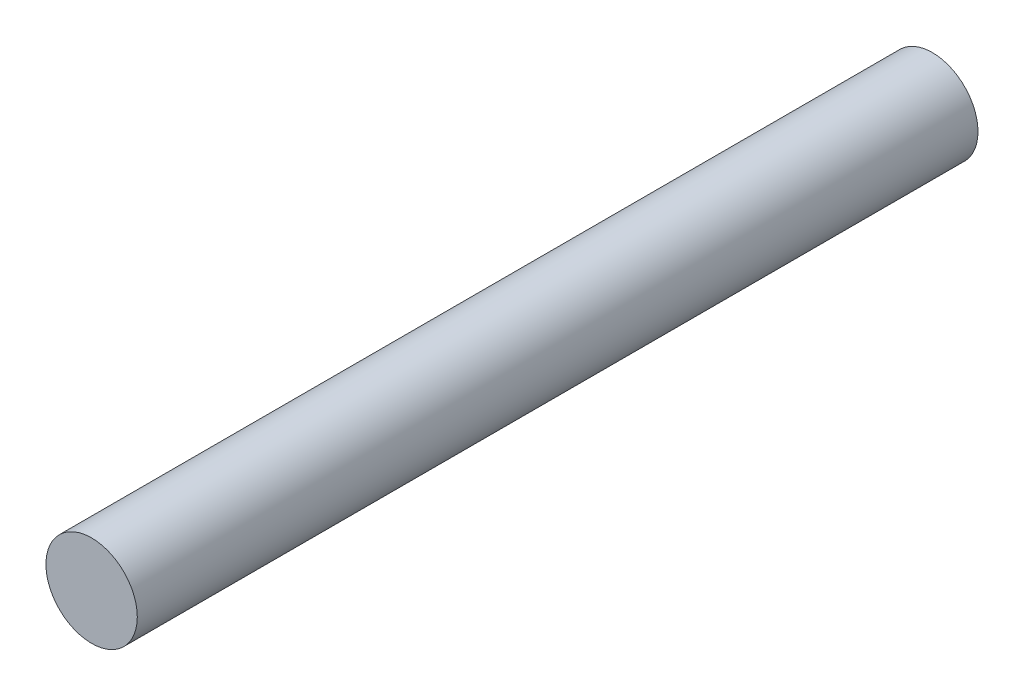
SolidWorks part; units mm, degrees
material "Custom Plastic"
ref_plane "Front Plane" through (0, 0, 0) normal (0, 0, 1) x (1, 0, 0)
ref_plane "Top Plane" through (0, 0, 0) normal (0, 1, 0) x (1, 0, 0)
ref_plane "Right Plane" through (0, 0, 0) normal (1, 0, 0) x (0, 0, -1)
sketch "Sketch1" plane through (0, 0, 0) normal (0, 0, 1) x (1, 0, 0)
  circle A0 centre (0, 0) radius 2.5
  dimension "D1" = 5
extrude "Boss-Extrude1" add sketch "Sketch1" along normal blind 46
